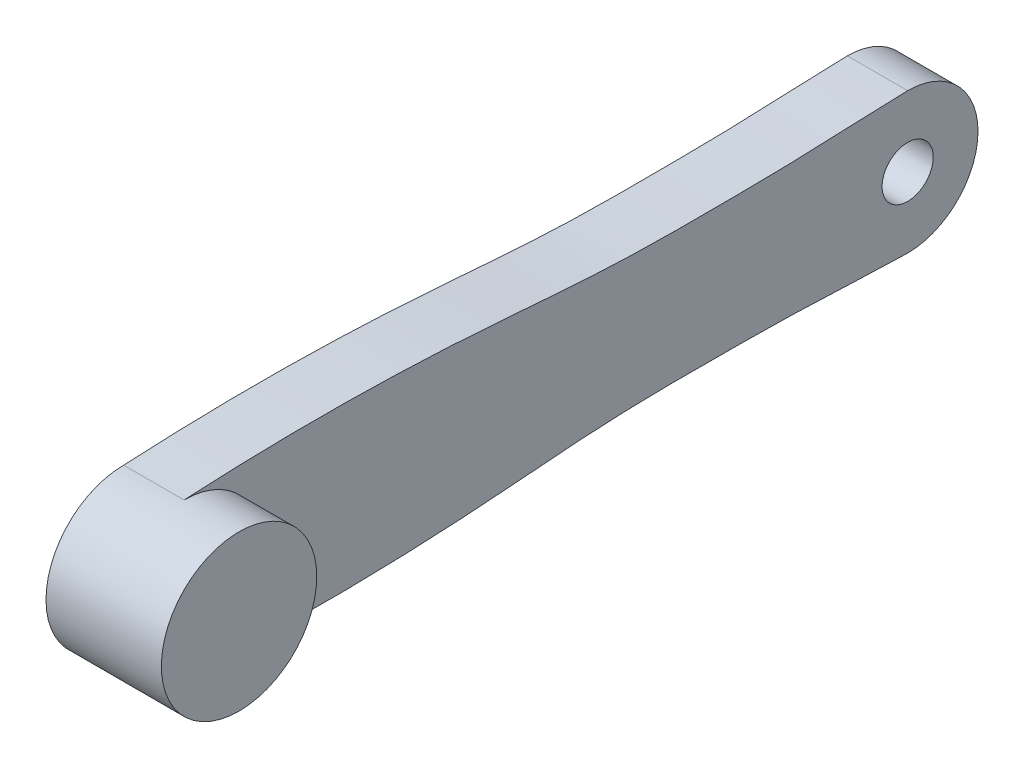
SolidWorks part; units mm, degrees
ref_plane "Front Plane" through (0, 0, 0) normal (0, 0, 1) x (1, 0, 0)
ref_plane "Top Plane" through (0, 0, 0) normal (0, 1, 0) x (1, 0, 0)
ref_plane "Right Plane" through (0, 0, 0) normal (1, 0, 0) x (0, 0, -1)
sketch "Sketch1" plane through (0, 0, 0) normal (1, 0, 0) x (0, 0, -1)
  circle A0 centre (0, 0) radius 18.225
  dimension "D1" = 36.45
extrude "Boss-Extrude1" add sketch "Sketch1" along normal blind 27.06
sketch "Sketch2" plane through (0, 0, 0) normal (-1, 0, 0) x (0, 0, 1)
  line L1 (4.6188, 0) -> (2.3094, 4)
  line L2 (2.3094, 4) -> (-2.3094, 4)
  line L3 (-2.3094, 4) -> (-4.6188, 0)
  line L4 (-4.6188, 0) -> (-2.3094, -4)
  line L5 (-2.3094, -4) -> (2.3094, -4)
  line L6 (2.3094, -4) -> (4.6188, 0)
  circle A0 centre (0, 0) radius 4 construction
  dimension "D1" = 8
extrude "Cut-Extrude1" cut sketch "Sketch2" against normal blind 5.8
sketch "Sketch3" plane through (0, 0, 0) normal (-1, 0, 0) x (0, 0, 1)
  line L0 (-169.75, 0) -> (0, 0) construction
  line L1 (-149.75, 15.75) -> (-149.75, -15.75) construction
  line L2 (-139.75, 15.425) -> (-139.75, -15.425) construction
  line L3 (-129.75, 15.3) -> (-129.75, -15.3) construction
  line L4 (-99.75, 15.65) -> (-99.75, -15.65) construction
  line L5 (-69.75, 17.775) -> (-69.75, -17.775) construction
  line L6 (-39.75, 19.025) -> (-39.75, -19.025) construction
  circle A0 centre (0, 0) radius 11 construction
  circle A1 centre (-169.75, 0) radius 10 construction
  arc A3 (-169.75, 16.5) -> (-169.75, -16.5) centre (-169.75, 0) ccw
  circle A4 centre (0, 0) radius 18.225 construction
  arc A5 (0, 18.225) -> (0, -18.225) centre (0, 0) ccw
  spline S0 degree 3 poles (-169.75, 16.5) (-159.749, 16.2703) (-146.423, 15.4355) (-123.0845, 15.2408) (-99.7009, 15.1468) (-56.5828, 19.333) (-23.2343, 19.4875) (0, 18.225) knots 0 0 0 0 0.176708 0.235577 0.412183 0.589219 1 1 1 1
  spline S1 degree 3 poles (-169.75, -16.5) (-159.749, -16.2703) (-146.423, -15.4355) (-123.0845, -15.2408) (-99.7009, -15.1468) (-56.5828, -19.333) (-23.2343, -19.4875) (0, -18.225) knots 0 0 0 0 0.176708 0.235577 0.412183 0.589219 1 1 1 1
  point P5 (-159.75, 0)
  point P6 (-11, 0)
  point P9 (-149.75, 15.75)
  point P10 (-149.75, -15.75)
  point P13 (-149.75, 0)
  point P14 (-139.75, 15.425)
  point P15 (-139.75, -15.425)
  point P18 (-139.75, 0)
  point P19 (-129.75, 15.3)
  point P20 (-129.75, -15.3)
  point P23 (-129.75, 0)
  point P26 (-99.75, 0)
  point P29 (-69.75, 0)
  point P32 (-39.75, 0)
  dimension "D1" = 22
  dimension "D3" = 20
  dimension "D4" = 16.5
  dimension "D17" = 169.8985
  dimension "D2" = 148.75
  dimension "D5" = 10
  dimension "D6" = 31.5
  dimension "D7" = 30.85
  dimension "D8" = 20
  dimension "D9" = 30.6
  dimension "D10" = 30
  dimension "D11" = 31.3
  dimension "D12" = 60
  dimension "D13" = 35.55
  dimension "D14" = 90
  dimension "D15" = 38.05
  dimension "D16" = 120
extrude "Boss-Extrude2" add sketch "Sketch3" against normal blind 14.15
hole_wizard "Tap Drill for M14x2.0 Tap1" positions "Sketch5" profile "Sketch7" hole size "M14x2.0" standard "ANSI Metric" end condition through all
sketch "Sketch5" plane through (0, 0, 0) normal (-1, 0, 0) x (0, 0, 1)
  point P0 (-169.75, 0)
sketch "Sketch7" plane through (0, 0, -169.75) normal (0, 1, 0) x (0, 0, 1)
  line L0 (0, 0) -> (0, 27.06)
  line L1 (0, 27.06) -> (6, 27.06)
  line L2 (6, 27.06) -> (6, 0)
  line L5 (6, 0) -> (0, 0)
  line L11 (0, -6.35) -> (0, 107.95) construction
  dimension "Thru Hole Dia." = 12
  dimension "Thru Hole Depth" = 27.06
sketch "Sketch8" plane through (0, 0, 0) normal (-1, 0, 0) x (0, 0, 1)
  circle A0 centre (-169.75, 0) radius 10
  dimension "D1" = 20
extrude "Cut-Extrude2" cut sketch "Sketch8" against normal blind 2.5
sketch "Sketch9" plane through (0, 0, 0) normal (-1, 0, 0) x (0, 0, 1)
  line L0 (0, 0) -> (-169.75, 0) construction
